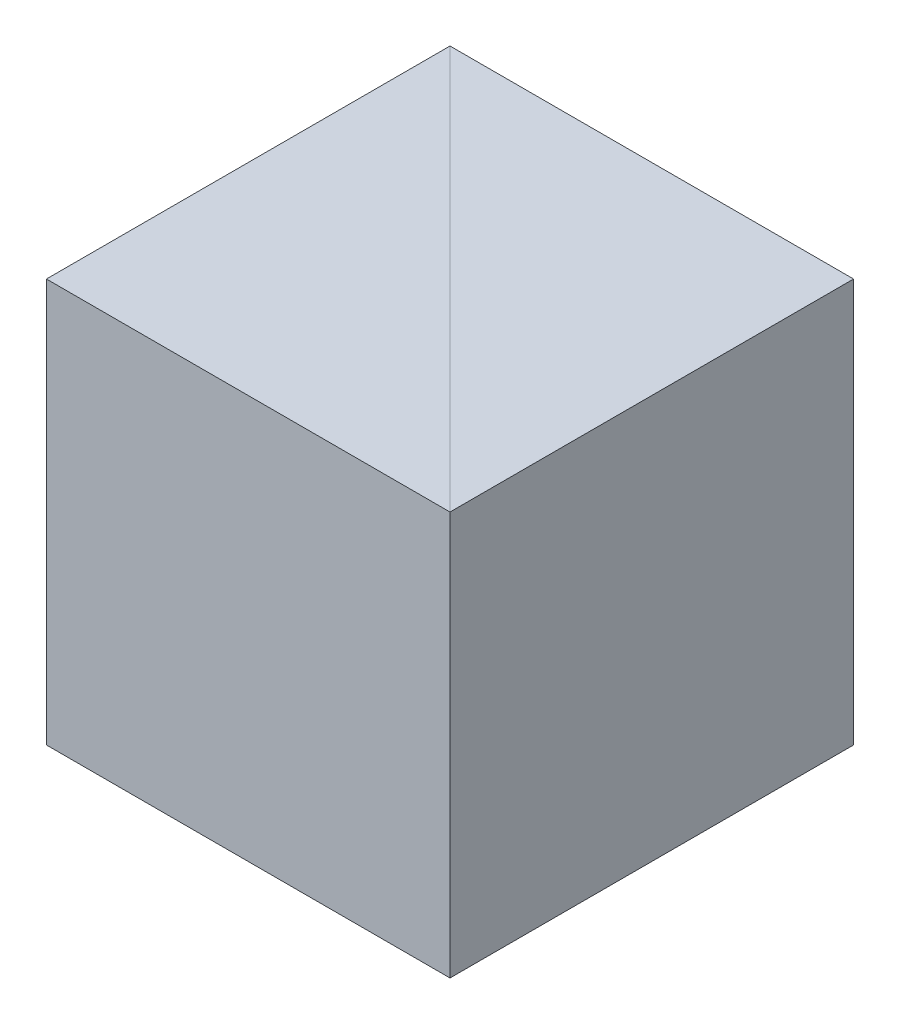
SolidWorks part; units mm, degrees
ref_plane "前视基准面" through (0, 0, 0) normal (0, 0, 1) x (1, 0, 0)
ref_plane "上视基准面" through (0, 0, 0) normal (0, 1, 0) x (1, 0, 0)
ref_plane "右视基准面" through (0, 0, 0) normal (1, 0, 0) x (0, 0, -1)
sketch "草图1" plane through (0, 0, 0) normal (0, 1, 0) x (1, 0, 0)
  line L0 (0, 0) -> (0, 25.4)
  line L1 (0, 25.4) -> (25.4, 0)
  line L2 (25.4, 0) -> (0, 0)
  dimension "D1" = 25.4
  dimension "D2" = 25.4
extrude "凸台-拉伸1" add sketch "草图1" along normal blind 25.4
sketch "草图2" plane through (0, 0, 0) normal (0, -1, 0) x (1, 0, 0)
  line L0 (0, -25.4) -> (25.4, -25.4)
  line L1 (25.4, -25.4) -> (25.4, 0)
  line L2 (25.4, 0) -> (0, -25.4)
extrude "凸台-拉伸2" add sketch "草图2" against normal blind 25.4 separate body
